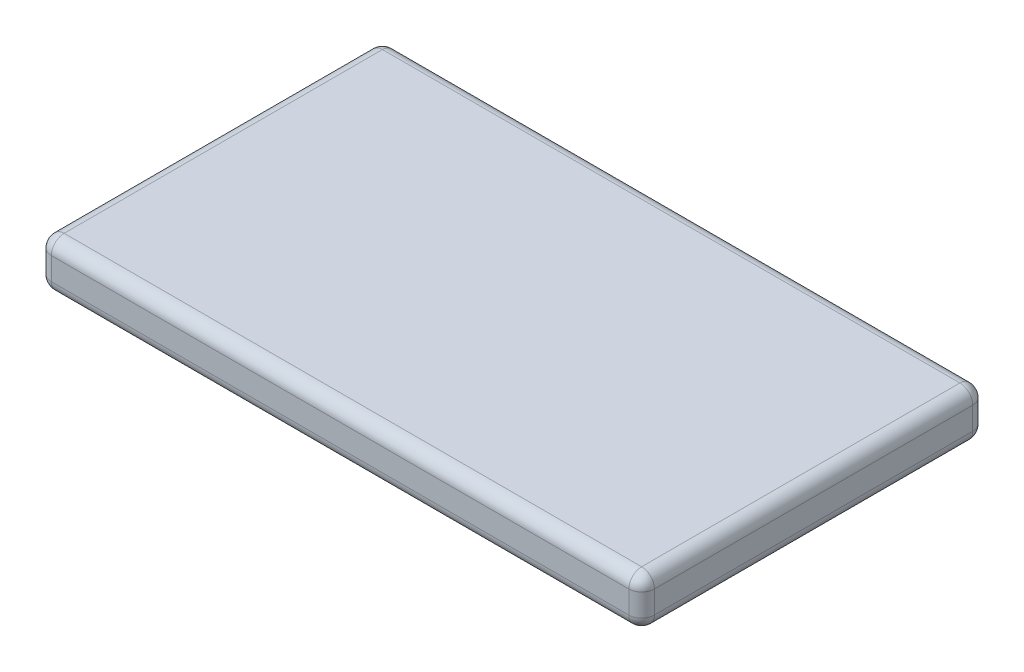
SolidWorks part; units mm, degrees
ref_plane "Front Plane" through (0, 0, 0) normal (0, 0, 1) x (1, 0, 0)
ref_plane "Top Plane" through (0, 0, 0) normal (0, 1, 0) x (1, 0, 0)
ref_plane "Right Plane" through (0, 0, 0) normal (1, 0, 0) x (0, 0, -1)
sketch "Sketch1" plane through (0, 0, 0) normal (0, 1, 0) x (1, 0, 0)
  line L1 (0, 0) -> (59.69, 0)
  line L2 (0, 0) -> (0, 34.036)
  line L3 (0, 34.036) -> (59.69, 34.036)
  line L4 (59.69, 0) -> (59.69, 34.036)
  dimension "D1" = 59.69
  dimension "D2" = 34.036
extrude "Boss-Extrude1" add sketch "Sketch1" along normal blind 4.7752
fillet "Fillet1" radius 1.27 12 edges at (0, 4.7752, -17.018) (0, 0, -17.018) (29.845, 4.7752, -34.036) (0, 2.3876, -34.036) (29.845, 0, -34.036) (59.69, 4.7752, -17.018) (59.69, 2.3876, -34.036) (59.69, 0, -17.018) (0, 2.3876, 0) (29.845, 4.7752, 0) (59.69, 2.3876, 0) (29.845, 0, 0)
